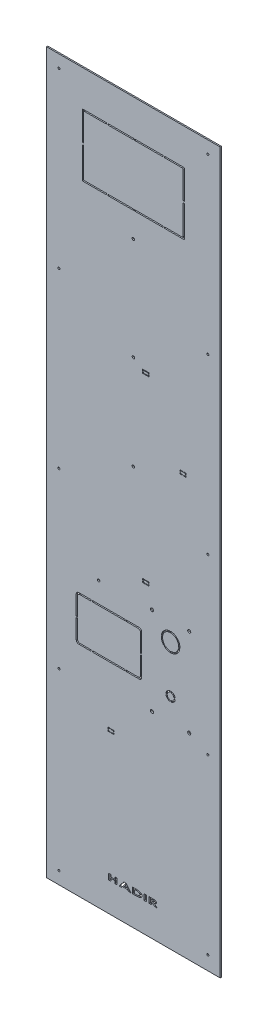
SolidWorks part; units mm, degrees
ref_plane "Front Plane" through (0, 0, 0) normal (0, 0, 1) x (1, 0, 0)
ref_plane "Top Plane" through (0, 0, 0) normal (0, 1, 0) x (1, 0, 0)
ref_plane "Right Plane" through (0, 0, 0) normal (1, 0, 0) x (0, 0, -1)
sketch "Sketch2" plane through (0, 0, 0) normal (0, 0, 1) x (1, 0, 0)
  line L0 (140, 680) -> (100, 680) construction
  line L5 (0, -480) -> (0, 680) construction
  line L6 (-140, 0) -> (140, 0) construction
  line L7 (100, 680) -> (100, 750.5127) construction
  line L8 (100, 750.5127) -> (100, -538.4561) construction
  line L9 (-140, 680) -> (-100, 680) construction
  line L10 (-100, 680) -> (-100, 750.5127) construction
  line L11 (-100, 750.5127) -> (-100, -538.4561) construction
  line L12 (-140, 680) -> (-140, 150) construction
  line L14 (-140, 680) -> (140, 680)
  line L15 (140, 680) -> (140, 580)
  line L17 (-140, -480) -> (140, -480)
  line L19 (140, -480) -> (140, 580)
  line L20 (-140, -480) -> (-140, 680)
  line L21 (-140, 150) -> (140, 150) construction
  line L22 (140, 150) -> (140, 110) construction
  line L23 (140, 110) -> (-140, 110) construction
  line L24 (0, 680) -> (0, 640) construction
  line L25 (-197.3636, 640) -> (197.5047, 640) construction
  line L26 (0, -480) -> (0, -440) construction
  line L27 (197.5047, -440) -> (-197.3636, -440) construction
  point P0 (0, 0)
  dimension "D1" = 1160
extrude "Boss-Extrude2" add sketch "Sketch2" along normal blind 2
sketch "Sketch3" plane through (0, 0, 0) normal (0, 0, 1) x (1, 0, 0)
  line L0 (120, 660) -> (120, 380.6) construction
  line L2 (-140, 660) -> (-120, 660) construction
  line L3 (120, 380.6) -> (-120, 380.6) construction
  line L4 (-120, 660) -> (-120, 680) construction
  line L5 (120, -457.6) -> (120, 101.2) construction
  line L6 (120, 101.2) -> (-120, 101.2) construction
  line L7 (-120, 680) -> (-120, 150) construction
  line L8 (-198.9172, 110) -> (186.996, 110) construction
  line L9 (-140, -480) -> (-100, -480) construction
  line L10 (60, -163) -> (90, -163) construction
  line L11 (0, 481.6) -> (0, 316.5) construction
  line L12 (-198.9172, 150) -> (186.996, 150) construction
  line L13 (0, 316.5) -> (0, 304.5) construction
  line L14 (186.996, 150) -> (186.996, 110) construction
  line L16 (60, -163) -> (30, -163) construction
  line L17 (-56.1, -21) -> (-56.1, -23) construction
  line L20 (-140, 680) -> (140, 680) construction
  line L22 (0, 640) -> (0, 623.18) construction
  line L23 (140, 660) -> (120, 660) construction
  line L24 (-56.1, 150) -> (-56.1, 110) construction
  line L25 (60, -21) -> (60, -36) construction
  line L26 (60, 0) -> (60, -21) construction
  line L27 (60, -21) -> (90, -21) construction
  line L28 (60, -127) -> (60, -163) construction
  line L29 (90, -163) -> (90, -21) construction
  line L30 (30, -163) -> (30, -21) construction
  line L31 (30, -21) -> (60, -21) construction
  line L127 (-140, 680) -> (-140, 640) construction
  line L132 (60, -36) -> (60, -38)
  line L137 (59.0006, -36.0333) -> (59.1224, -38.0297)
  line L222 (59.958, -51.042) -> (70.6066, -40.3934) construction
  line L223 (59.958, -51.042) -> (70.5575, -61.6415) construction
  line L224 (60, -51) -> (50.8076, -41.8076) construction
  line L225 (59.958, -51.042) -> (49.3934, -61.6066) construction
  line L230 (74.9337, -52.4092) -> (72.9425, -52.2213)
  line L231 (74.8066, -53.4011) -> (72.8324, -53.0809)
  line L232 (60, -66) -> (60, -64)
  line L233 (59.0005, -65.9671) -> (59.0005, -63.9615)
  line L250 (67.5, -127) -> (52.5, -127) construction
  line L251 (60, -127) -> (60, -119.5) construction
  line L252 (60, -119.5) -> (60, -121.5) construction
  line L253 (67.5, -127) -> (65.5, -127) construction
  line L254 (65.5, -127) -> (60, -127) construction
  line L255 (60, -127) -> (60, -132.5) construction
  line L256 (60, -127) -> (54.6967, -121.6967) construction
  line L257 (60, -127) -> (65.3033, -132.3033) construction
  line L258 (60, -127) -> (54.6967, -132.3033) construction
  line L259 (60, -127) -> (65.3033, -121.6967) construction
  line L260 (60.9806, -119.5644) -> (60.7191, -121.5472)
  line L261 (67.4356, -126.0194) -> (65.4528, -126.2809)
  line L262 (58.9874, -119.5687) -> (59.2574, -121.5504)
  line L263 (67.4356, -127.9806) -> (65.4528, -127.7191)
  line L264 (52.5644, -126.0194) -> (54.5472, -126.2809)
  line L265 (52.5644, -127.9806) -> (54.5472, -127.7191)
  line L266 (58.9874, -134.4313) -> (59.2574, -132.4496)
  line L267 (60.9806, -134.4356) -> (60.7191, -132.4528)
  line L268 (45.2633, -48.202) -> (47.2282, -48.5751)
  line L269 (45.1082, -49.202) -> (47.0937, -49.4417)
  line L270 (49.0202, -40.7803) -> (50.4841, -42.1429)
  line L271 (48.3636, -41.5346) -> (49.9151, -42.7966)
  line L272 (48.3636, -60.4655) -> (49.9151, -59.2034)
  line L273 (49.3934, -61.6066) -> (50.8076, -60.1924)
  line L274 (69.988, -62.191) -> (68.6563, -60.6989)
  line L275 (69.2202, -62.8317) -> (67.9908, -61.2541)
  line L276 (69.5589, -39.4403) -> (68.2844, -40.9816)
  line L277 (70.3079, -40.1029) -> (68.9335, -41.5558)
  line L295 (-32.1, -221.1) -> (-35.6, -221.1)
  line L304 (120, -457.6) -> (120, -178.2) construction
  line L305 (120, -178.2) -> (-120, -178.2) construction
  line L306 (100, 784.4571) -> (100, -643.8463) construction
  line L310 (30, -92) -> (13.48, -92) construction
  line L311 (-140, 640) -> (140, 640) construction
  line L314 (-140, -480) -> (-140, -440) construction
  line L315 (-140, -440) -> (140, -440) construction
  line L320 (-100, -480) -> (-100, 680) construction
  line L338 (-120, -480) -> (-120, -460) construction
  line L339 (-120, -460) -> (-140, -460) construction
  line L340 (13.48, -60) -> (13.48, -91)
  line L341 (120, -478.8) -> (120, -457.6) construction
  line L372 (120, -457.6) -> (140, -457.6) construction
  line L373 (9.48, -128) -> (-11.5164, -128)
  line L374 (140, 680) -> (140, 580) construction
  line L375 (120, 660) -> (120, 680) construction
  line L421 (0, 316.5) -> (0, 164.1) construction
  line L423 (0, 164.1) -> (0, 152.1) construction
  line L430 (0, 164.1) -> (80, 164.1) construction
  line L433 (0, 24.4) -> (0, 12.4) construction
  line L439 (0, -480) -> (0, 680) construction
  line L457 (0, 12.4) -> (20, 12.4) construction
  line L459 (24, 14.3) -> (24, 12.9)
  line L478 (0, 304.5) -> (20, 304.5) construction
  line L511 (-40.1, -221.1) -> (-40.1, -222.5)
  line L530 (25, 15.3) -> (20.5, 15.3)
  line L532 (25, 15.3) -> (25, 12.9)
  line L535 (-31.1, -220.1) -> (-35.6, -220.1)
  line L536 (-31.1, -220.1) -> (-31.1, -222.5)
  line L557 (24, 306.4) -> (24, 305)
  line L559 (25, 307.4) -> (20.5, 307.4)
  line L578 (80, 164.1) -> (80, 194.1) construction
  line L579 (84, 196) -> (84, 194.6)
  line L589 (-31.1, -225.9) -> (-35.6, -225.9)
  line L590 (-41.1, -220.1) -> (-41.1, -222.5)
  line L601 (25, 9.5) -> (20.5, 9.5)
  line L603 (15, 15.3) -> (15, 12.9)
  line L605 (20, 9.5) -> (20, 15.3) construction
  line L607 (25, 12.4) -> (15, 12.4) construction
  line L609 (24, 10.5) -> (20.5, 10.5)
  line L611 (16, 14.3) -> (16, 12.9)
  line L613 (24, 14.3) -> (20.5, 14.3)
  line L614 (19.5, 10.5) -> (16, 10.5)
  line L615 (-36.1, -224.9) -> (-36.1, -220.1) construction
  line L616 (-31.1, -223) -> (-41.1, -223) construction
  line L617 (-32.1, -224.9) -> (-35.6, -224.9)
  line L618 (-32.1, -221.1) -> (-32.1, -222.5)
  line L619 (-40.1, -223.5) -> (-40.1, -224.9)
  line L621 (-36.6, -224.9) -> (-40.1, -224.9)
  line L622 (-32.1, -223.5) -> (-32.1, -224.9)
  line L623 (-31.1, -223.5) -> (-32.1, -223.5)
  line L624 (-31.1, -222.5) -> (-32.1, -222.5)
  line L625 (-35.6, -220.1) -> (-35.6, -221.1)
  line L626 (-36.6, -220.1) -> (-36.6, -221.1)
  line L627 (-35.6, -224.9) -> (-35.6, -225.9)
  line L628 (-36.6, -224.9) -> (-36.6, -225.9)
  line L629 (-40.1, -222.5) -> (-41.1, -222.5)
  line L630 (-40.1, -223.5) -> (-41.1, -223.5)
  line L631 (-36.6, -220.1) -> (-41.1, -220.1)
  line L632 (-31.1, -220.1) -> (-41.1, -220.1) construction
  line L633 (-36.6, -221.1) -> (-40.1, -221.1)
  line L634 (-32.1, -221.1) -> (-40.1, -221.1) construction
  line L635 (-32.1, -224.9) -> (-40.1, -224.9) construction
  line L636 (-36.6, -225.9) -> (-41.1, -225.9)
  line L637 (-31.1, -225.9) -> (-41.1, -225.9) construction
  line L638 (-31.1, -223.5) -> (-31.1, -225.9)
  line L639 (-31.1, -220.1) -> (-31.1, -225.9) construction
  line L640 (-32.1, -221.1) -> (-32.1, -224.9) construction
  line L641 (-40.1, -221.1) -> (-40.1, -224.9) construction
  line L642 (-41.1, -223.5) -> (-41.1, -225.9)
  line L643 (-41.1, -220.1) -> (-41.1, -225.9) construction
  line L709 (-140, 680) -> (-140, -480) construction
  line L724 (81.2, 622.2) -> (50.0052, 622.2)
  line L726 (82.2, 621.2) -> (82.2, 575.26)
  line L729 (81.2, 521.6) -> (50.0052, 521.6)
  line L730 (-82.2, 522.6) -> (-82.2, 572.28)
  line L732 (79.2, 620.2) -> (50.0052, 620.2)
  line L734 (-80.2, 524.6) -> (-80.2, 572.28)
  line L741 (79.2, 523.6) -> (50.0052, 523.6)
  line L743 (80.2, 619.2) -> (80.2, 575.26)
  line L746 (-0.015, 523.6) -> (-41.1248, 523.6)
  line L747 (48.0052, 620.2) -> (1.985, 620.2)
  line L748 (1.985, 622.2) -> (1.985, 620.2)
  line L749 (-0.015, 622.2) -> (-0.015, 620.2)
  line L750 (1.985, 523.6) -> (1.985, 521.6)
  line L751 (-0.015, 523.6) -> (-0.015, 521.6)
  line L752 (-41.1248, 622.2) -> (-41.1248, 620.2)
  line L753 (-41.1248, 523.6) -> (-41.1248, 521.6)
  line L754 (-0.015, 620.2) -> (-41.1248, 620.2)
  line L755 (-43.1248, 622.2) -> (-43.1248, 620.2)
  line L756 (-43.1248, 523.6) -> (-43.1248, 521.6)
  line L757 (50.0052, 622.2) -> (50.0052, 620.2)
  line L758 (50.0052, 523.6) -> (50.0052, 521.6)
  line L759 (80.2, 572.28) -> (80.2, 524.6)
  line L760 (48.0052, 622.2) -> (48.0052, 620.2)
  line L761 (48.0052, 523.6) -> (48.0052, 521.6)
  line L762 (140, 680) -> (-140, 680) construction
  line L763 (82.2, 572.28) -> (80.2, 572.28)
  line L764 (140, -480) -> (140, 680) construction
  line L765 (82.2, 575.26) -> (80.2, 575.26)
  line L766 (-80.2, 575.26) -> (-82.2, 575.26)
  line L767 (-80.2, 572.28) -> (-82.2, 572.28)
  line L768 (-82.2, 575.26) -> (-82.2, 621.2)
  line L769 (-82.2, 521.6) -> (-82.2, 622.2) construction
  line L770 (-80.2, 575.26) -> (-80.2, 619.2)
  line L771 (-80.2, 523.6) -> (-80.2, 620.2) construction
  line L772 (-43.1248, 622.2) -> (-81.2, 622.2)
  line L773 (82.2, 622.2) -> (-82.2, 622.2) construction
  line L774 (-43.1248, 620.2) -> (-79.2, 620.2)
  line L775 (80.2, 620.2) -> (-80.2, 620.2) construction
  line L776 (-43.1248, 523.6) -> (-79.2, 523.6)
  line L777 (80.2, 523.6) -> (-80.2, 523.6) construction
  line L778 (-43.1248, 521.6) -> (-81.2, 521.6)
  line L779 (82.2, 521.6) -> (-82.2, 521.6) construction
  line L780 (-0.015, 622.2) -> (-41.1248, 622.2)
  line L781 (-0.015, 521.6) -> (-41.1248, 521.6)
  line L782 (48.0052, 622.2) -> (1.985, 622.2)
  line L783 (48.0052, 523.6) -> (1.985, 523.6)
  line L784 (48.0052, 521.6) -> (1.985, 521.6)
  line L785 (82.2, 572.28) -> (82.2, 522.6)
  line L786 (82.2, 622.2) -> (82.2, 521.6) construction
  line L787 (80.2, 620.2) -> (80.2, 523.6) construction
  line L788 (-92.12, -124) -> (-92.12, -93)
  line L789 (-88.12, -56) -> (-68, -56)
  line L790 (11.48, -62) -> (11.48, -91)
  line L791 (7.48, -126) -> (-11.5164, -126)
  line L792 (-90.12, -122) -> (-90.12, -93)
  line L793 (-86.12, -58) -> (-68, -58)
  line L794 (13.48, -128) -> (-92.12, -128) construction
  line L795 (-92.12, -128) -> (-92.12, -56) construction
  line L796 (11.48, -126) -> (-90.12, -126) construction
  line L797 (-90.12, -126) -> (-90.12, -58) construction
  line L798 (-92.12, -56) -> (13.48, -56) construction
  line L799 (-90.12, -58) -> (11.48, -58) construction
  line L800 (13.48, -56) -> (13.48, -128) construction
  line L801 (11.48, -58) -> (11.48, -126) construction
  line L802 (-39.32, -56) -> (-38.32, -56) construction
  line L803 (-39.32, -56) -> (-40.32, -56) construction
  line L804 (-11.5164, -56) -> (-11.5164, -58)
  line L805 (-11.5164, -126) -> (-11.5164, -128)
  line L806 (13.48, -93) -> (13.48, -124)
  line L807 (-13.5164, -56) -> (-13.5164, -58)
  line L809 (-90.12, -93) -> (-92.12, -93)
  line L810 (-0.015, 521.6) -> (0, 481.6) construction
  line L811 (-90.12, -91) -> (-92.12, -91)
  line L812 (-90.12, -91) -> (-90.12, -62)
  line L813 (-92.12, -91) -> (-92.12, -60)
  line L814 (13.48, -93) -> (11.48, -93)
  line L815 (13.48, -91) -> (11.48, -91)
  line L816 (-13.5164, -126) -> (-13.5164, -128)
  line L817 (-68, -56) -> (-68, -58)
  line L818 (-68, -126) -> (-68, -128)
  line L819 (-11.5164, -56) -> (9.48, -56)
  line L820 (-66, -56) -> (-66, -58)
  line L821 (-66, -126) -> (-66, -128)
  line L822 (-66, -56) -> (-13.5164, -56)
  line L823 (-66, -58) -> (-13.5164, -58)
  line L824 (-68, -126) -> (-86.12, -126)
  line L825 (-68, -128) -> (-88.12, -128)
  line L826 (-11.5164, -58) -> (7.48, -58)
  line L827 (-13.5164, -126) -> (-66, -126)
  line L828 (-13.5164, -128) -> (-66, -128)
  line L829 (11.48, -93) -> (11.48, -122)
  line L843 (25, 307.4) -> (25, 305)
  line L845 (25, 301.6) -> (20.5, 301.6)
  line L846 (15, 307.4) -> (15, 305)
  line L848 (20, 301.6) -> (20, 307.4) construction
  line L849 (25, 304.5) -> (15, 304.5) construction
  line L851 (24, 302.6) -> (20.5, 302.6)
  line L852 (16, 306.4) -> (16, 305)
  line L854 (24, 306.4) -> (20.5, 306.4)
  line L858 (85, 197) -> (80.5, 197)
  line L859 (24, 10.5) -> (16, 10.5) construction
  line L865 (85, 197) -> (85, 194.6)
  line L867 (85, 191.2) -> (80.5, 191.2)
  line L868 (75, 197) -> (75, 194.6)
  line L870 (80, 191.2) -> (80, 197) construction
  line L872 (85, 194.1) -> (75, 194.1) construction
  line L874 (84, 192.2) -> (80.5, 192.2)
  line L876 (76, 196) -> (76, 194.6)
  line L877 (84, 196) -> (80.5, 196)
  line L878 (19.5, 302.6) -> (16, 302.6)
  line L879 (24, 302.6) -> (16, 302.6) construction
  line L880 (15, 12.9) -> (16, 12.9)
  line L881 (15, 11.9) -> (16, 11.9)
  line L882 (20.5, 15.3) -> (20.5, 14.3)
  line L883 (19.5, 15.3) -> (19.5, 14.3)
  line L884 (20.5, 10.5) -> (20.5, 9.5)
  line L885 (19.5, 10.5) -> (19.5, 9.5)
  line L886 (24, 12.9) -> (25, 12.9)
  line L887 (24, 11.9) -> (25, 11.9)
  line L888 (25, 11.9) -> (25, 9.5)
  line L889 (25, 15.3) -> (25, 9.5) construction
  line L890 (24, 11.9) -> (24, 10.5)
  line L891 (24, 14.3) -> (24, 10.5) construction
  line L892 (19.5, 14.3) -> (16, 14.3)
  line L893 (24, 14.3) -> (16, 14.3) construction
  line L894 (19.5, 15.3) -> (15, 15.3)
  line L895 (25, 15.3) -> (15, 15.3) construction
  line L896 (19.5, 9.5) -> (15, 9.5)
  line L897 (25, 9.5) -> (15, 9.5) construction
  line L898 (16, 11.9) -> (16, 10.5)
  line L899 (16, 14.3) -> (16, 10.5) construction
  line L900 (15, 11.9) -> (15, 9.5)
  line L901 (15, 15.3) -> (15, 9.5) construction
  line L902 (19.5, 306.4) -> (16, 306.4)
  line L903 (79.5, 192.2) -> (76, 192.2)
  line L904 (25, 305) -> (24, 305)
  line L905 (25, 304) -> (24, 304)
  line L906 (15, 305) -> (16, 305)
  line L907 (15, 304) -> (16, 304)
  line L908 (20.5, 307.4) -> (20.5, 306.4)
  line L909 (19.5, 307.4) -> (19.5, 306.4)
  line L910 (20.5, 302.6) -> (20.5, 301.6)
  line L911 (19.5, 302.6) -> (19.5, 301.6)
  line L912 (25, 304) -> (25, 301.6)
  line L913 (25, 307.4) -> (25, 301.6) construction
  line L914 (24, 304) -> (24, 302.6)
  line L915 (24, 306.4) -> (24, 302.6) construction
  line L916 (24, 306.4) -> (16, 306.4) construction
  line L917 (19.5, 307.4) -> (15, 307.4)
  line L918 (25, 307.4) -> (15, 307.4) construction
  line L919 (19.5, 301.6) -> (15, 301.6)
  line L920 (25, 301.6) -> (15, 301.6) construction
  line L921 (16, 304) -> (16, 302.6)
  line L922 (16, 306.4) -> (16, 302.6) construction
  line L923 (15, 304) -> (15, 301.6)
  line L924 (15, 307.4) -> (15, 301.6) construction
  line L926 (79.5, 197) -> (75, 197)
  line L927 (85, 197) -> (75, 197) construction
  line L928 (85, 194.6) -> (84, 194.6)
  line L929 (85, 193.6) -> (84, 193.6)
  line L930 (80.5, 197) -> (80.5, 196)
  line L931 (79.5, 197) -> (79.5, 196)
  line L932 (80.5, 192.2) -> (80.5, 191.2)
  line L933 (79.5, 192.2) -> (79.5, 191.2)
  line L934 (76, 194.6) -> (75, 194.6)
  line L935 (76, 193.6) -> (75, 193.6)
  line L936 (84, 193.6) -> (84, 192.2)
  line L937 (84, 196) -> (84, 192.2) construction
  line L938 (85, 193.6) -> (85, 191.2)
  line L939 (85, 197) -> (85, 191.2) construction
  line L940 (79.5, 196) -> (76, 196)
  line L941 (84, 196) -> (76, 196) construction
  line L942 (84, 192.2) -> (76, 192.2) construction
  line L943 (79.5, 191.2) -> (75, 191.2)
  line L944 (85, 191.2) -> (75, 191.2) construction
  line L945 (76, 193.6) -> (76, 192.2)
  line L946 (76, 196) -> (76, 192.2) construction
  line L947 (75, 193.6) -> (75, 191.2)
  line L948 (75, 197) -> (75, 191.2) construction
  circle A27 centre (-56.1, -23) radius 2
  arc A80 (60.9806, -119.5644) -> (67.4356, -126.0194) centre (60, -127) cw
  arc A96 (67.4356, -127.9806) -> (60.9806, -134.4356) centre (60, -127) cw
  arc A99 (58.9874, -134.4313) -> (52.5644, -127.9806) centre (60, -127) cw
  arc A109 (58.9874, -119.5687) -> (52.5644, -126.0194) centre (60, -127) ccw
  arc A110 (60.7191, -121.5472) -> (65.4528, -126.2809) centre (60, -127) cw
  arc A111 (65.4528, -127.7191) -> (60.7191, -132.4528) centre (60, -127) cw
  arc A112 (59.2574, -132.4496) -> (54.5472, -127.7191) centre (60, -127) cw
  arc A113 (54.5472, -126.2809) -> (59.2574, -121.5504) centre (60, -127) cw
  arc A121 (70.3079, -40.1029) -> (74.9337, -52.4092) centre (60, -51) cw
  circle A122 centre (-120, -460) radius 1.65
  arc A123 (68.9335, -41.5558) -> (72.9425, -52.2213) centre (60, -51) cw
  arc A124 (72.8324, -53.0809) -> (68.6563, -60.6989) centre (60, -51) cw
  arc A125 (74.8066, -53.4011) -> (69.988, -62.191) centre (60, -51) cw
  arc A126 (69.2202, -62.8317) -> (60, -66) centre (60, -51) cw
  arc A127 (67.9908, -61.2541) -> (60, -64) centre (60, -51) cw
  arc A128 (59.0005, -63.9615) -> (50.8076, -60.1924) centre (60, -51) cw
  arc A129 (59.0005, -65.9671) -> (49.3934, -61.6066) centre (60.0005, -51.0005) cw
  arc A130 (49.9151, -59.2034) -> (47.0937, -49.4417) centre (60, -51) cw
  arc A131 (48.3636, -60.4655) -> (45.1082, -49.202) centre (60, -51) cw
  arc A132 (47.2282, -48.5751) -> (49.9151, -42.7966) centre (60, -51) cw
  arc A133 (45.2633, -48.202) -> (48.3636, -41.5346) centre (60, -51) cw
  arc A134 (50.4841, -42.1429) -> (59.1224, -38.0297) centre (60, -51) cw
  arc A135 (59.0006, -36.0333) -> (49.0202, -40.7803) centre (60, -51) ccw
  arc A136 (60, -36) -> (69.5589, -39.4403) centre (60, -51) cw
  arc A137 (60, -38) -> (68.2844, -40.9816) centre (60, -51) cw
  circle A138 centre (120, -457.6) radius 1.65
  circle A140 centre (90, -21) radius 2.5
  circle A141 centre (90, -163) radius 2.5
  circle A142 centre (30, -163) radius 2.5
  circle A143 centre (30, -21) radius 2.5
  circle A144 centre (-120, 660) radius 1.65
  circle A145 centre (120, 660) radius 1.65
  circle A146 centre (-120, 380.6) radius 1.65
  circle A147 centre (120, 380.6) radius 1.65
  circle A152 centre (120, -178.2) radius 1.65
  circle A153 centre (-120, -178.2) radius 1.65
  circle A154 centre (120, 101.2) radius 1.65
  circle A155 centre (-120, 101.2) radius 1.65
  arc A158 (-81.2, 521.6) -> (-82.2, 522.6) centre (-81.2, 522.6) cw
  arc A159 (-80.2, 524.6) -> (-79.2, 523.6) centre (-79.2, 524.6) ccw
  arc A160 (-81.2, 622.2) -> (-82.2, 621.2) centre (-81.2, 621.2) ccw
  arc A161 (-79.2, 620.2) -> (-80.2, 619.2) centre (-79.2, 619.2) ccw
  arc A162 (82.2, 522.6) -> (81.2, 521.6) centre (81.2, 522.6) cw
  arc A163 (79.2, 523.6) -> (80.2, 524.6) centre (79.2, 524.6) ccw
  arc A164 (79.2, 620.2) -> (80.2, 619.2) centre (79.2, 619.2) cw
  arc A165 (81.2, 622.2) -> (82.2, 621.2) centre (81.2, 621.2) cw
  arc A166 (-88.12, -128) -> (-92.12, -124) centre (-88.12, -124) cw
  arc A167 (-86.12, -126) -> (-90.12, -122) centre (-86.12, -122) cw
  arc A168 (-92.12, -60) -> (-88.12, -56) centre (-88.12, -60) cw
  arc A169 (-90.12, -62) -> (-86.12, -58) centre (-86.12, -62) cw
  arc A170 (13.48, -124) -> (9.48, -128) centre (9.48, -124) cw
  arc A171 (11.48, -122) -> (7.48, -126) centre (7.48, -122) cw
  arc A172 (11.48, -62) -> (7.48, -58) centre (7.48, -62) ccw
  arc A173 (13.48, -60) -> (9.48, -56) centre (9.48, -60) ccw
  circle A174 centre (0, 481.6) radius 2
  circle A175 centre (0, 316.5) radius 2
  circle A177 centre (0, 164.1) radius 2
  point P56 (0, 623.18)
  point P126 (-36.1, -223)
  point P186 (13.48, -92)
  point P234 (-92.12, -108.5)
  point P251 (60, -51)
  point P323 (0, 623.18)
  point P411 (-82.2, 598.23)
  dimension "D8" = 2
  dimension "D9" = 530
  dimension "D10" = 3.3
  dimension "D11" = 4
  dimension "D12" = 105.6
  dimension "D13" = 2
  dimension "D14" = 5
  dimension "D15" = 15
  dimension "D16" = 21
  dimension "D17" = 5
  dimension "D18" = 72
  dimension "D19" = 5
  dimension "D20" = 279.4
  dimension "D21" = 4
  dimension "D24" = 4
  dimension "D25" = 5.8
  dimension "D37" = 279.4
  dimension "D44" = 10
  dimension "D39" = 279.4
  dimension "D40" = 5.8
  dimension "D53" = 5.8
  dimension "D57" = 10
  dimension "D60" = 1
  dimension "D61" = 100.6
  dimension "D62" = 1
  dimension "D54" = 45
  dimension "D56" = 45
  dimension "D63" = 164.4
  dimension "D66" = 57.8
  dimension "D67" = 57.8
  dimension "D55" = 1
  dimension "D48" = 1
  dimension "D68" = 1
  dimension "D69" = 57.8
  dimension "D30" = 3.3
  dimension "D31" = 3.3
  dimension "D46" = 1
  dimension "D36" = 5
  dimension "D26" = 3.3
  dimension "D27" = 3.3
  dimension "D28" = 3.3
  dimension "D22" = 4
  dimension "D23" = 3.3
  dimension "D32" = 3.3
  dimension "D33" = 3.3
  dimension "D41" = 3.3
  dimension "D58" = 2
  dimension "D64" = 4
  dimension "D43" = 5.8
  dimension "D29" = 279.4
  dimension "D34" = 40
  dimension "D35" = 10
  dimension "D38" = 1
  dimension "D42" = 10
  dimension "D45" = 1
  dimension "D50" = 1
  dimension "D52" = 1
  dimension "D59" = 16.82
  dimension "D70" = 1
  dimension "D71" = 1
extrude "Cut-Extrude8" cut sketch "Sketch3" along normal blind 2
sketch "Sketch4" plane through (0, 0, 0) normal (0, 0, 1) x (1, 0, 0)
  line L0 (-121.7889, -433.1206) -> (118.2111, -433.1206) construction
  text T0 "<b>HADIR</b>" font "Century Gothic" height in points 36
extrude "Cut-Extrude9" cut sketch "Sketch4" along normal blind 2
